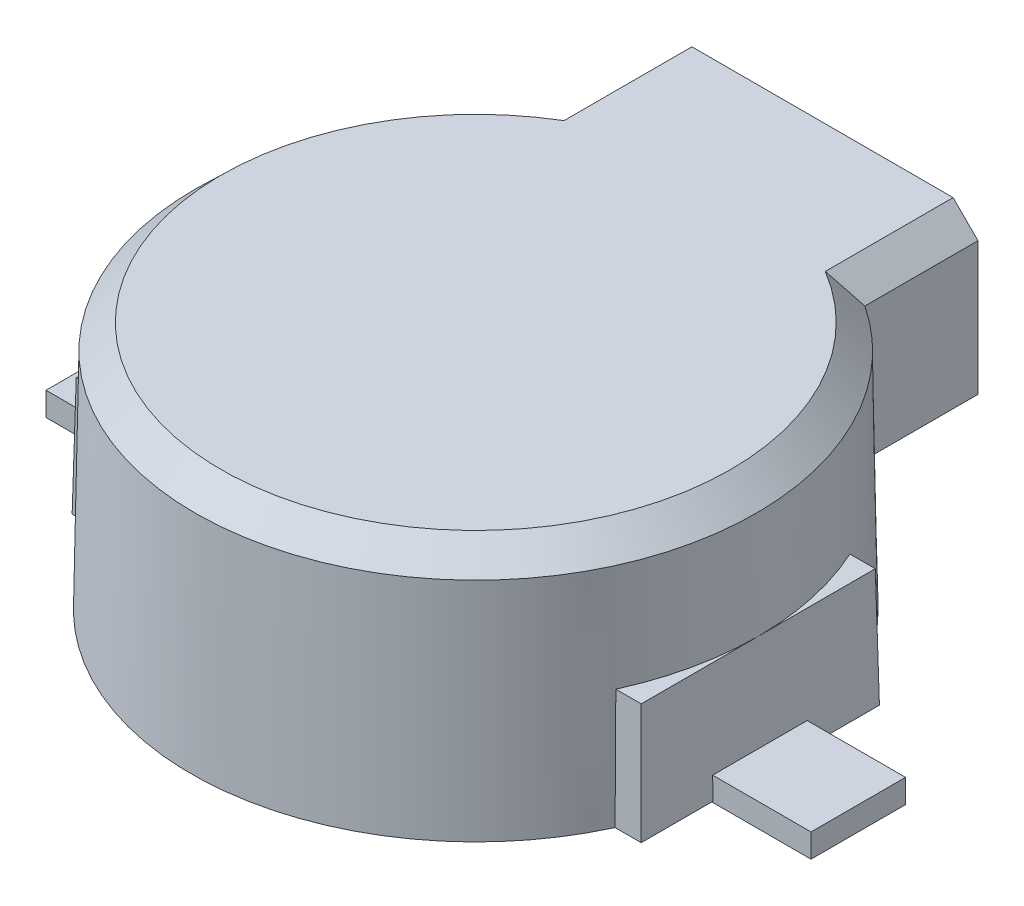
SolidWorks part; units mm, degrees
ref_plane "Front Plane" through (0, 0, 0) normal (0, 0, 1) x (1, 0, 0)
ref_plane "Top Plane" through (0, 0, 0) normal (0, 1, 0) x (1, 0, 0)
ref_plane "Right Plane" through (0, 0, 0) normal (1, 0, 0) x (0, 0, -1)
sketch "Sketch1" plane through (0, 0, 0) normal (0, 1, 0) x (1, 0, 0)
  circle A0 centre (0, 0) radius 4.575
  dimension "D1" = 9.15
extrude "Extrude1" add sketch "Sketch1" along normal blind 4 draft 1
sketch "Sketch2" plane through (0, 0, 0) normal (0, 1, 0) x (1, 0, 0)
  line L1 (-4.575, -1.915) -> (4.575, -1.915)
  line L2 (-4.575, -1.915) -> (-4.575, 1.915)
  line L3 (-4.575, 1.915) -> (4.575, 1.915)
  line L4 (4.575, -1.915) -> (4.575, 1.915)
  circle A0 centre (0, 0) radius 4.575 construction
  point P6 (4.575, 0)
  dimension "D1" = 3.83
extrude "Extrude2" add sketch "Sketch2" along normal blind 1.9 draft 1
sketch "Sketch3" plane through (0, 0, 0) normal (0, 1, 0) x (1, 0, 0)
  line L0 (4.575, 1.915) -> (4.1549, 1.915) construction
  line L1 (-2.5, 5.575) -> (2.5, 5.575)
  line L2 (-2.5, 5.575) -> (-2.5, 1.915)
  line L3 (-2.5, 1.915) -> (2.5, 1.915)
  line L4 (2.5, 5.575) -> (2.5, 1.915)
  arc A0 (-4.1549, -1.915) -> (4.1549, -1.915) centre (0, 0) ccw construction
  point P4 (0, 1.915)
  dimension "D1" = 5
  dimension "D2" = 5.575
extrude "Extrude3" add sketch "Sketch3" along normal up to surface (2.54 mm away) from offset 1.46 up to face at (0, 4, 4.5052)
sketch "Sketch4" plane through (0, 0, -5.575) normal (0, 0, -1) x (-1, 0, 0)
  line L1 (-0.2, 1.81) -> (0.2, 1.81)
  line L2 (-0.2, 1.81) -> (-0.2, 1.46)
  line L3 (-0.2, 1.46) -> (0.2, 1.46)
  line L4 (0.2, 1.81) -> (0.2, 1.46)
  line L6 (-2.5, 1.46) -> (2.5, 1.46) construction
  point P4 (0, 1.46)
  dimension "D1" = 0.4
  dimension "D2" = 0.35
extrude "Cut-Extrude1" cut sketch "Sketch4" against normal up to vertex (10.114 mm away)
sketch "Sketch5" plane through (0, 0, 0) normal (0, 0, 1) x (1, 0, 0)
  line L0 (2.5, 4) -> (-2.5, 4) construction
  line L1 (1.75, 3.5) -> (-1.75, 3.5)
  line L2 (1.75, 3.5) -> (1.75, 2.8)
  line L3 (1.75, 2.8) -> (-1.75, 2.8)
  line L4 (-1.75, 3.5) -> (-1.75, 2.8)
  point P6 (0, 2.8)
  dimension "D1" = 3.5
  dimension "D2" = 0.7
  dimension "D3" = 0.5
extrude "Cut-Extrude2" cut sketch "Sketch5" against normal through all
chamfer "Chamfer1" distance 0.4 angle 45 3 edges at (-2.5, 4, -4.6614) (2.5, 4, -4.6614) (0, 4, 4.5052)
sketch "Sketch6" plane through (0, 0, 0) normal (0, -1, 0) x (1, 0, 0)
  line L0 (1.25, 0.76) -> (-1.25, 0.76) construction
  line L1 (6.15, -0.76) -> (1.25, -0.76)
  line L2 (6.15, -0.76) -> (6.15, 0.76)
  line L3 (6.15, 0.76) -> (1.25, 0.76)
  line L4 (1.25, -0.76) -> (1.25, 0.76)
  line L5 (-1.25, -0.76) -> (-6.15, -0.76)
  line L6 (-1.25, -0.76) -> (-1.25, 0.76)
  line L7 (-1.25, 0.76) -> (-6.15, 0.76)
  line L8 (-6.15, -0.76) -> (-6.15, 0.76)
  point P8 (1.25, 0)
  point P10 (0, 0.76)
  dimension "D1" = 1.52
  dimension "D2" = 2.5
  dimension "D3" = 12.3
extrude "Extrude4" add sketch "Sketch6" against normal blind 0.36 and the other way blind 0.02
sketch "Component_Outline" plane through (0, 0, 0) normal (0, 1, 0) x (1, 0, 0)
  line L0 (-4.1549, -1.915) -> (-4.575, -1.915)
  line L1 (-4.575, -1.915) -> (-4.575, -0.76)
  line L2 (-4.575, -0.76) -> (-6.15, -0.76)
  line L4 (-6.15, -0.76) -> (-6.15, 0.76)
  line L6 (-6.15, 0.76) -> (-4.575, 0.76)
  line L7 (-4.575, 0.76) -> (-4.575, 1.915)
  line L8 (-4.575, 1.915) -> (-4.1549, 1.915)
  line L9 (-2.5, 3.8315) -> (-2.5, 5.575)
  line L10 (-2.5, 5.575) -> (-2.5, 3.8011) construction
  line L11 (-2.5, 5.575) -> (2.5, 5.575)
  line L13 (2.5, 5.575) -> (2.5, 3.8315)
  line L14 (2.5, 3.8011) -> (2.5, 5.575) construction
  line L15 (4.1549, 1.915) -> (4.575, 1.915)
  line L16 (4.575, 1.915) -> (4.575, 0.76)
  line L17 (4.575, 0.76) -> (6.15, 0.76)
  line L18 (6.15, 0.76) -> (6.15, -0.76)
  line L19 (6.15, -0.76) -> (4.575, -0.76)
  line L20 (4.575, -0.76) -> (4.575, -1.915)
  line L21 (4.575, -1.915) -> (4.1549, -1.915)
  arc A1 (-4.1549, -1.915) -> (2.5, 3.8315) centre (0, 0) ccw
  arc A2 (-2.5, 3.8315) -> (-4.1549, 1.915) centre (0, 0) ccw
